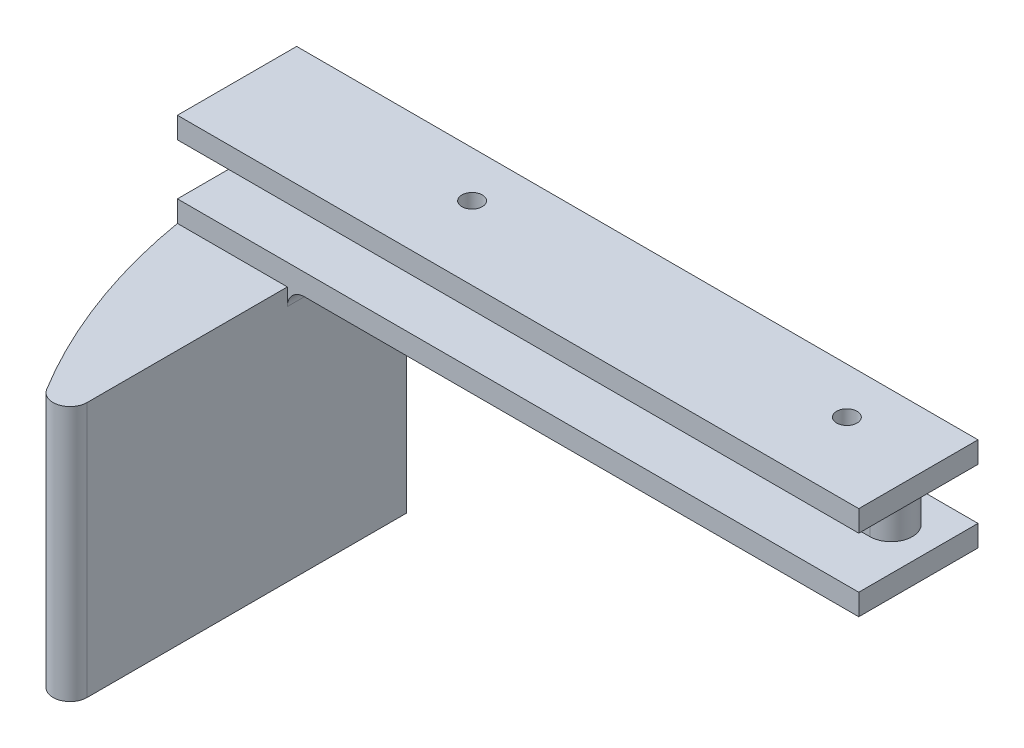
SolidWorks part; units mm, degrees
ref_plane "Front Plane" through (0, 0, 0) normal (0, 0, 1) x (1, 0, 0)
ref_plane "Top Plane" through (0, 0, 0) normal (0, 1, 0) x (1, 0, 0)
ref_plane "Right Plane" through (0, 0, 0) normal (1, 0, 0) x (0, 0, -1)
sketch "Sketch2" plane through (0, 0, 0) normal (0, 1, 0) x (1, 0, 0)
  line L1 (0, 0) -> (101.6, 0)
  line L2 (0, 0) -> (0, 17.78)
  line L3 (0, 17.78) -> (101.6, 17.78)
  line L4 (101.6, 0) -> (101.6, 17.78)
  dimension "D1" = 17.78
  dimension "D2" = 101.6
extrude "Boss-Extrude1" add sketch "Sketch2" along normal blind 3.175
sketch "Sketch3" plane through (0, 0, 0) normal (0, -1, 0) x (1, 0, 0)
  line L0 (95.25, -11.176) -> (6.35, -11.176) construction
  line L1 (95.25, -14.351) -> (6.35, -14.351)
  line L2 (95.25, -8.001) -> (6.35, -8.001)
  line L3 (0, 0) -> (101.6, 0) construction
  line L4 (0, -17.78) -> (0, 0) construction
  arc A0 (95.25, -14.351) -> (95.25, -8.001) centre (95.25, -11.176) ccw
  arc A1 (6.35, -8.001) -> (6.35, -14.351) centre (6.35, -11.176) ccw
  point P2 (50.8, -11.176)
  dimension "D1" = 88.9
  dimension "D2" = 11.176
  dimension "D3" = 6.35
  dimension "D4" = 6.35
extrude "Boss-Extrude2" add sketch "Sketch3" along normal blind 7.62 contours L2 A1 L1 A0
ref_plane "Plane1" through (0, -3.81, 0) normal (0, -1, 0) x (-1, 0, 0)
mirror "Mirror1" about plane through (0, -3.81, 0) normal (0, -1, 0) of "Boss-Extrude1"
sketch "Sketch4" plane through (0, -10.795, 0) normal (0, -1, 0) x (1, 0, 0)
  line L0 (0, 0) -> (101.6, 0) construction
  line L1 (0, -17.78) -> (16.3938, -17.78)
  line L2 (0, -17.78) -> (0, 0)
  line L4 (16.3938, -17.78) -> (16.3938, 0)
  line L5 (16.3938, 0) -> (16.3938, 38.1)
  arc A0 (0, 0) -> (16.3938, 38.1) centre (86.3751, -14.5889) cw
  dimension "D2" = 87.5984
  dimension "D1" = 38.1
  dimension "D3" = 17.78
  dimension "D4" = 16.3938
extrude "Boss-Extrude3" add sketch "Sketch4" along normal blind 38.1
fillet "Fillet1" radius 2.54 1 edges at (16.3938, -10.795, -8.89)
fillet "Fillet2" radius 2.54 1 edges at (16.3938, -29.845, 38.1)
sketch "Sketch5" plane through (0, -10.795, 0) normal (0, -1, 0) x (-1, 0, 0)
  line L0 (-101.6, 0) -> (-101.6, 17.78) construction
  line L2 (-101.6, 17.78) -> (-18.9338, 17.78) construction
  circle A0 centre (-88.9, 10.922) radius 1.524
  circle A1 centre (-33.02, 10.922) radius 1.524
  dimension "D1" = 3.048
  dimension "D2" = 3.048
  dimension "D3" = 12.7
  dimension "D4" = 55.88
  dimension "D5" = 6.858
extrude "Cut-Extrude1" cut sketch "Sketch5" against normal through all
